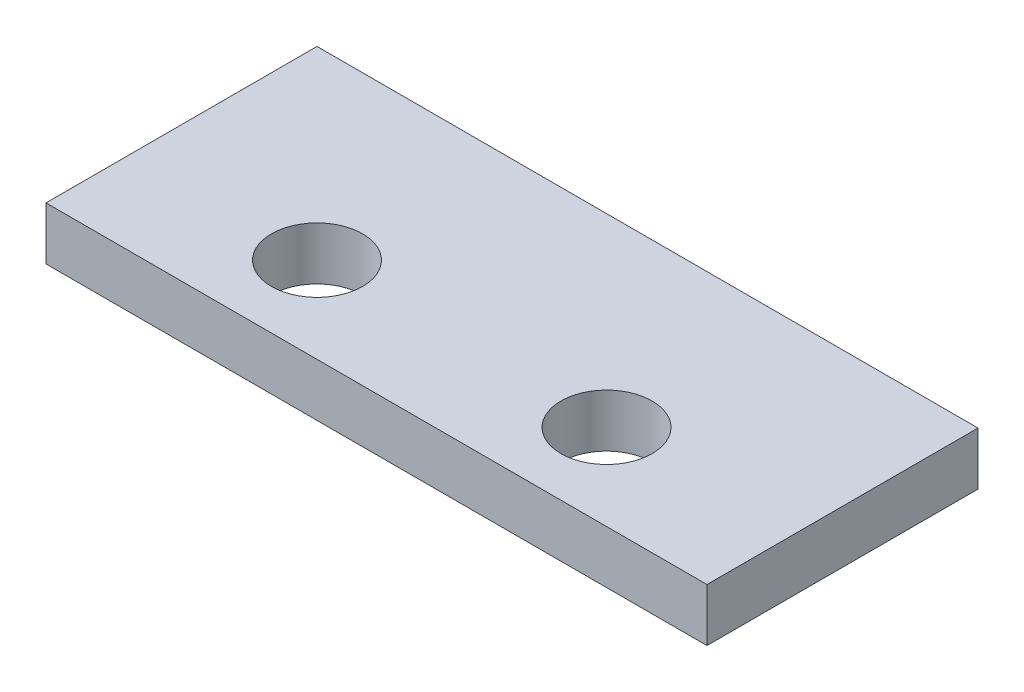
SolidWorks part; units mm, degrees
ref_plane "Front Plane" through (0, 0, 0) normal (0, 0, 1) x (1, 0, 0)
ref_plane "Top Plane" through (0, 0, 0) normal (0, 1, 0) x (1, 0, 0)
ref_plane "Right Plane" through (0, 0, 0) normal (1, 0, 0) x (0, 0, -1)
sketch "Sketch1" plane through (0, 0, 0) normal (0, 1, 0) x (1, 0, 0)
  line L1 (-11.6504, 2.529) -> (13.7496, 2.529)
  line L2 (-11.6504, 2.529) -> (-11.6504, -7.885)
  line L3 (-11.6504, -7.885) -> (13.7496, -7.885)
  line L4 (13.7496, 2.529) -> (13.7496, -7.885)
  circle A0 centre (-4.5384, -4.583) radius 1.7526
  circle A1 centre (6.5868, -4.583) radius 1.7526
  dimension "D3" = 3.5052
  dimension "D4" = 3.5052
  dimension "D5" = 11.1252
  dimension "D1" = 25.4
  dimension "D2" = 10.414
  dimension "D6" = 7.112
  dimension "D7" = 3.302
extrude "Boss-Extrude1" add sketch "Sketch1" along normal blind 2.032
equation "\"0..8in\"=0.1"
